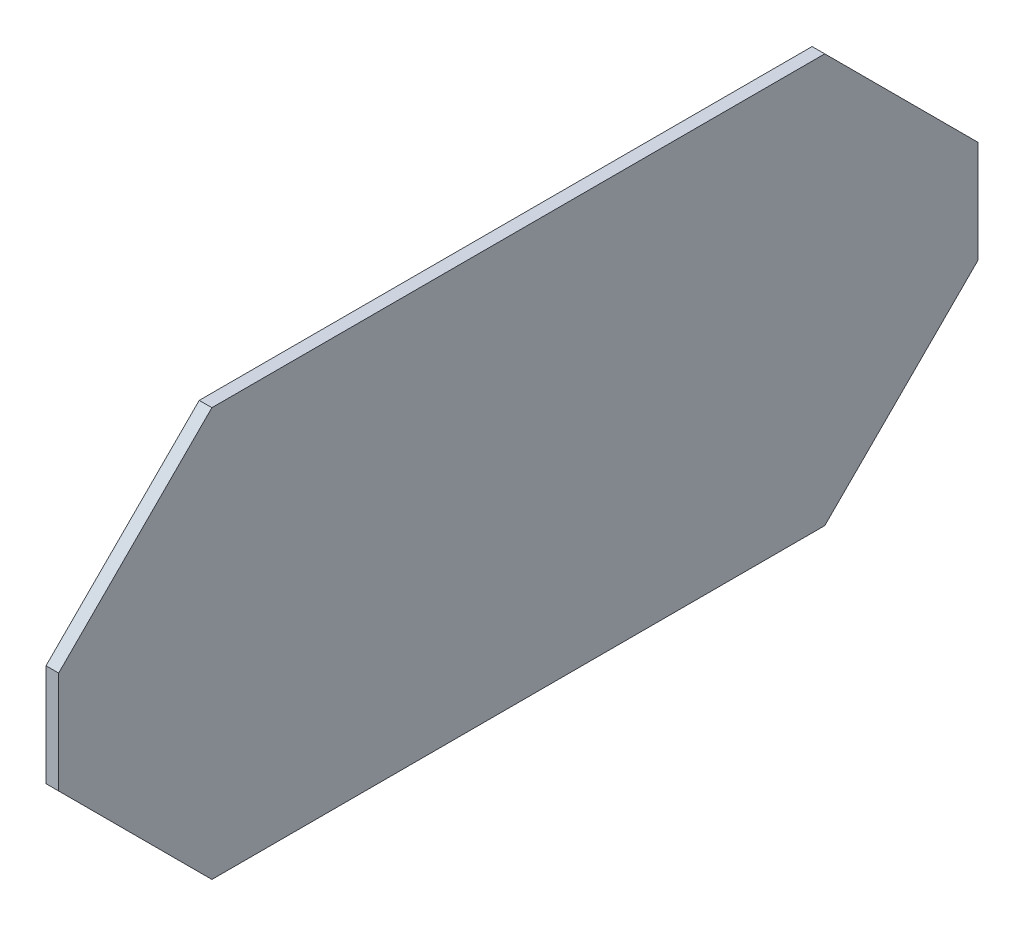
SolidWorks part; units mm, degrees
ref_plane "Front Plane" through (0, 0, 0) normal (0, 0, 1) x (1, 0, 0)
ref_plane "Top Plane" through (0, 0, 0) normal (0, 1, 0) x (1, 0, 0)
ref_plane "Right Plane" through (0, 0, 0) normal (1, 0, 0) x (0, 0, -1)
sketch "Sketch1" plane through (0, 0, 0) normal (0, 0, 1) x (1, 0, 0)
  line L1 (-0.3937, 12.7) -> (0.3937, 12.7)
  line L2 (-0.3937, 12.7) -> (-0.3937, -12.7)
  line L3 (-0.3937, -12.7) -> (0.3937, -12.7)
  line L4 (0.3937, 12.7) -> (0.3937, -12.7)
  line L5 (-0.3937, 12.7) -> (0.3937, -12.7) construction
  line L6 (-0.3937, -12.7) -> (0.3937, 12.7) construction
  point P0 (0, 0)
  dimension "D1" = 0.7874
  dimension "D2" = 25.4
extrude "McMaster 2636T21" add sketch "Sketch1" along normal mid plane 57.15
chamfer "Chamfer1" distance 9.525 angle 45 4 edges at (0, 12.7, -28.575) (0, -12.7, -28.575) (0, -12.7, 28.575) (0, 12.7, 28.575)
